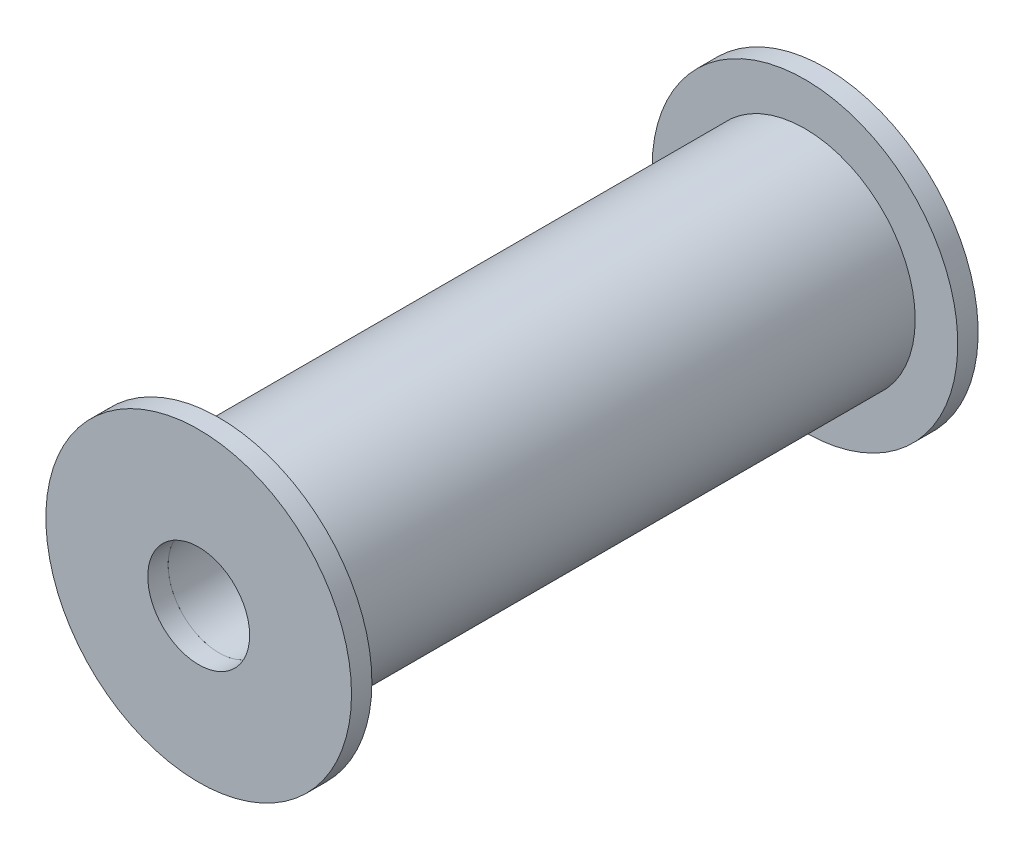
SolidWorks part; units mm, degrees
ref_plane "Front Plane" through (0, 0, 0) normal (0, 0, 1) x (1, 0, 0)
ref_plane "Top Plane" through (0, 0, 0) normal (0, 1, 0) x (1, 0, 0)
ref_plane "Right Plane" through (0, 0, 0) normal (1, 0, 0) x (0, 0, -1)
sketch "Sketch1" plane through (0, 0, 0) normal (0, 0, 1) x (1, 0, 0)
  circle A0 centre (0, 0) radius 21.6439
  circle A1 centre (0, 0) radius 10
extrude "Boss-Extrude1" add sketch "Sketch1" along normal blind 115
sketch "Sketch2" plane through (0, 0, 115) normal (0, 0, 1) x (1, 0, 0)
  circle A0 centre (0, 0) radius 10
  circle A1 centre (0, 0) radius 30
extrude "Boss-Extrude2" add sketch "Sketch2" along normal blind 4
sketch "Sketch3" plane through (0, 0, 0) normal (0, 0, -1) x (-1, 0, 0)
  circle A0 centre (0, 0) radius 10
  circle A1 centre (0, 0) radius 30
extrude "Boss-Extrude3" add sketch "Sketch3" along normal blind 4
